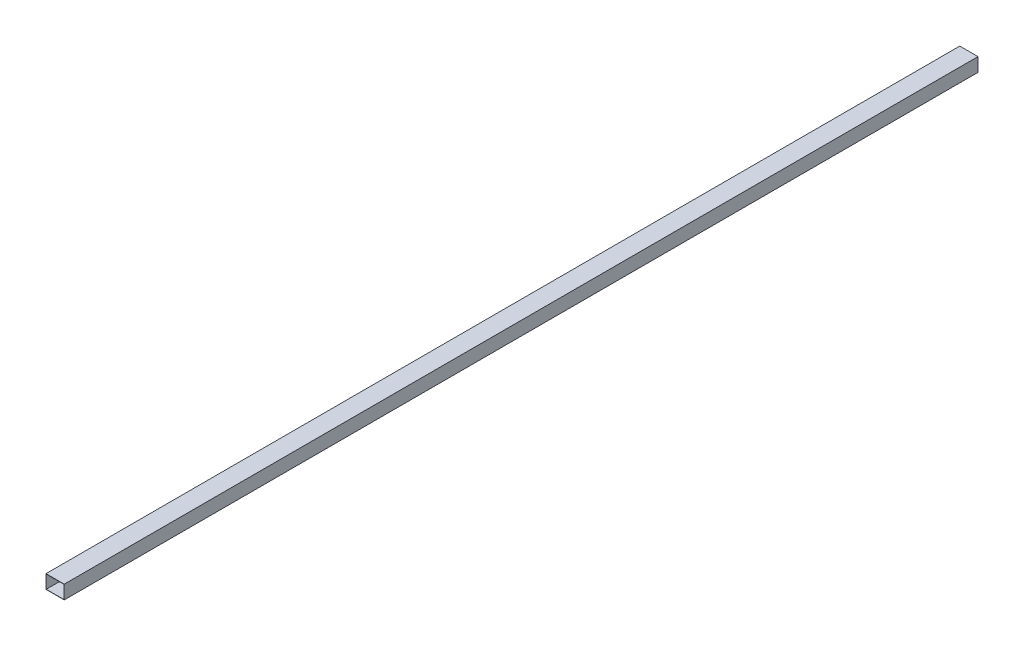
SolidWorks part; units mm, degrees
material "3.0205 (EN-AW 1200)"
ref_plane "Piano frontale" through (0, 0, 0) normal (0, 0, 1) x (1, 0, 0)
ref_plane "Piano superiore" through (0, 0, 0) normal (0, 1, 0) x (1, 0, 0)
ref_plane "Piano destro" through (0, 0, 0) normal (1, 0, 0) x (0, 0, -1)
sketch "Schizzo1" plane through (0, 0, 0) normal (0, 0, 1) x (1, 0, 0)
  line L1 (-20, 15) -> (20, 15)
  line L2 (-20, 15) -> (-20, -15)
  line L3 (-20, -15) -> (20, -15)
  line L4 (20, 15) -> (20, -15)
  line L5 (-20, 15) -> (20, -15) construction
  line L6 (-20, -15) -> (20, 15) construction
  line L7 (-19.5, -14.5) -> (19.5, -14.5)
  line L8 (-19.5, -14.5) -> (-19.5, 14.5)
  line L9 (-19.5, 14.5) -> (19.5, 14.5)
  line L10 (19.5, -14.5) -> (19.5, 14.5)
  line L11 (-19.5, -14.5) -> (19.5, 14.5) construction
  line L12 (-19.5, 14.5) -> (19.5, -14.5) construction
  point P0 (0, 0)
  point P6 (0, 0)
  dimension "D1" = 40
  dimension "D2" = 30
  dimension "D3" = 39
  dimension "D4" = 29
extrude "Estrusione-Estrusione1" add sketch "Schizzo1" along normal blind 2004
